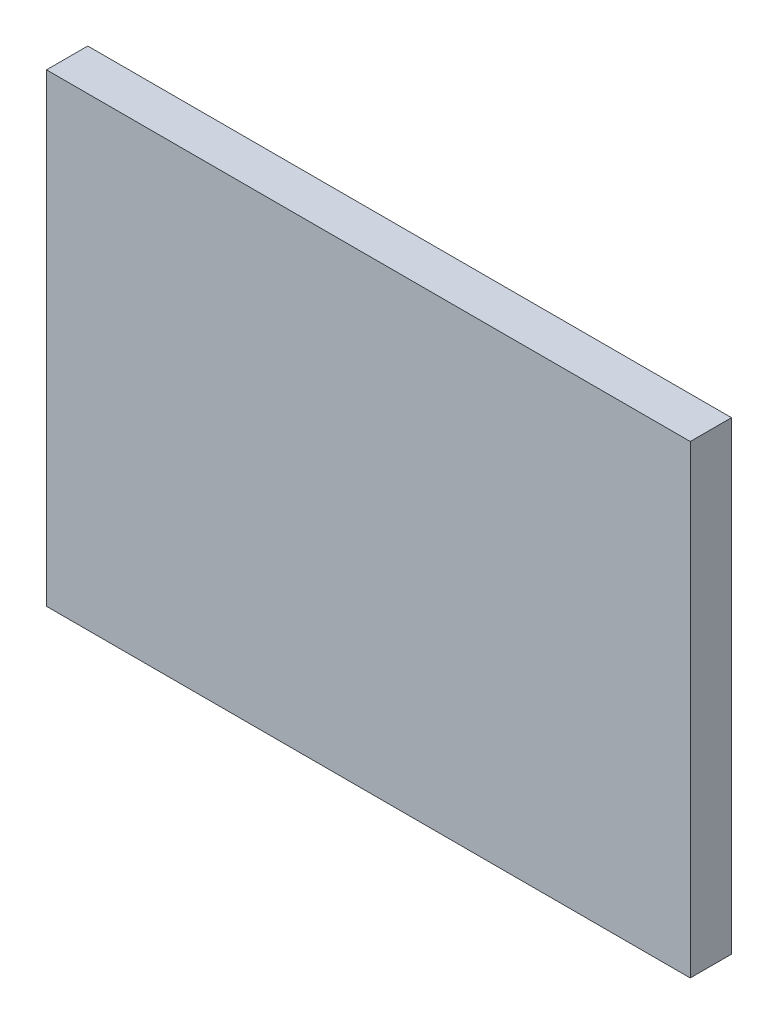
SolidWorks part; units mm, degrees
ref_plane "Front Plane" through (0, 0, 0) normal (0, 0, 1) x (1, 0, 0)
ref_plane "Top Plane" through (0, 0, 0) normal (0, 1, 0) x (1, 0, 0)
ref_plane "Right Plane" through (0, 0, 0) normal (1, 0, 0) x (0, 0, -1)
sketch "Sketch1" plane through (0, 0, 0) normal (0, 0, 1) x (1, 0, 0)
  line L1 (-29.65, 21.4) -> (29.65, 21.4)
  line L2 (-29.65, 21.4) -> (-29.65, -21.4)
  line L3 (-29.65, -21.4) -> (29.65, -21.4)
  line L4 (29.65, 21.4) -> (29.65, -21.4)
  line L5 (-29.65, 21.4) -> (29.65, -21.4) construction
  line L6 (-29.65, -21.4) -> (29.65, 21.4) construction
  point P0 (0, 0)
  dimension "D1" = 59.3
  dimension "D2" = 42.8
extrude "Boss-Extrude1" add sketch "Sketch1" along normal blind 3.8
sketch "Sketch2" plane through (0, 0, 3.8) normal (0, 0, 1) x (1, 0, 0)
  line L1 (-24.5, 18.5) -> (24.5, 18.5)
  line L2 (-24.5, 18.5) -> (-24.5, -18.5)
  line L3 (-24.5, -18.5) -> (24.5, -18.5)
  line L4 (24.5, 18.5) -> (24.5, -18.5)
  line L5 (-24.5, 18.5) -> (24.5, -18.5) construction
  line L6 (-24.5, -18.5) -> (24.5, 18.5) construction
  point P0 (0, 0)
  dimension "D1" = 49
  dimension "D2" = 37
